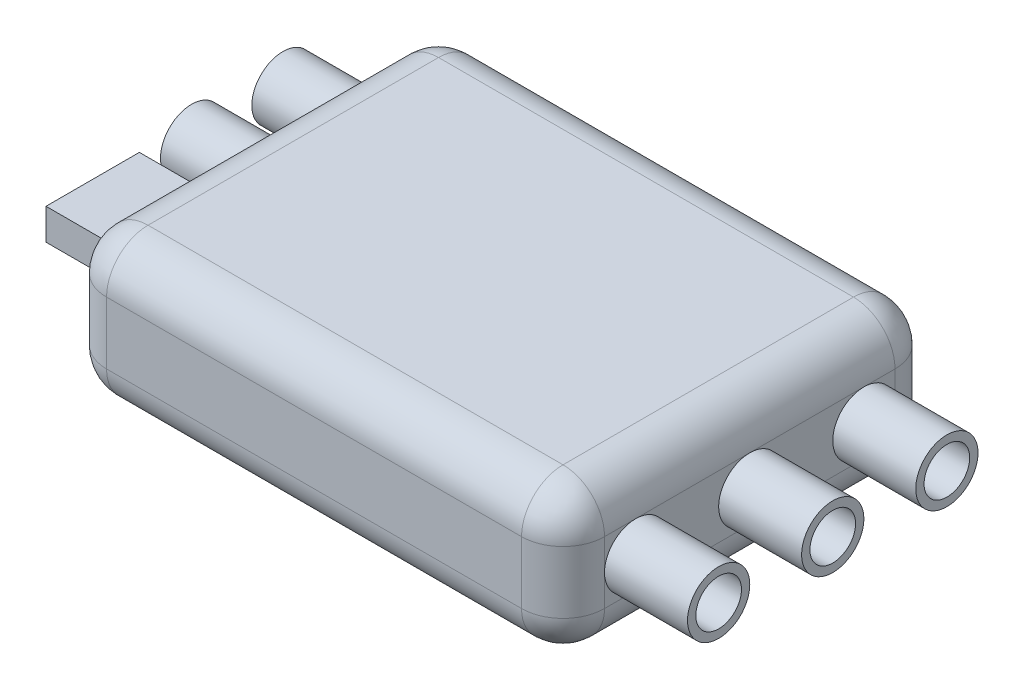
SolidWorks part; units mm, degrees
ref_plane "Front Plane" through (0, 0, 0) normal (0, 0, 1) x (1, 0, 0)
ref_plane "Top Plane" through (0, 0, 0) normal (0, 1, 0) x (1, 0, 0)
ref_plane "Right Plane" through (0, 0, 0) normal (1, 0, 0) x (0, 0, -1)
sketch "Sketch1" plane through (0, 0, 0) normal (0, 1, 0) x (1, 0, 0)
  line L1 (-10, -9) -> (10, -9)
  line L2 (-12, -7) -> (-12, 7)
  line L3 (-10, 9) -> (10, 9)
  line L4 (12, -7) -> (12, 7)
  line L5 (-12, -9) -> (12, 9) construction
  line L6 (-12, 9) -> (12, -9) construction
  arc A0 (-10, -9) -> (-12, -7) centre (-10, -7) cw
  arc A1 (10, 9) -> (12, 7) centre (10, 7) cw
  arc A2 (-12, 7) -> (-10, 9) centre (-10, 7) cw
  arc A3 (10, -9) -> (12, -7) centre (10, -7) ccw
  point P0 (0, 0)
  dimension "D3" = 2
  dimension "D4" = 2
  dimension "D1" = 24
  dimension "D2" = 18
extrude "Boss-Extrude1" add sketch "Sketch1" along normal blind 7
fillet "Fillet1" radius 2 16 edges at (0, 0, 9) (11.4142, 0, 8.4142) (12, 0, 0) (11.4142, 0, -8.4142) (0, 0, -9) (-11.4142, 0, -8.4142) (-12, 0, 0) (-11.4142, 0, 8.4142) (-12, 7, 0) (-11.4142, 7, -8.4142) (0, 7, -9) (11.4142, 7, -8.4142) (12, 7, 0) (11.4142, 7, 8.4142) (0, 7, 9) (-11.4142, 7, 8.4142)
sketch "Sketch2" plane through (12, 0, 0) normal (1, 0, 0) x (0, 0, -1)
  line L0 (7, 3.5) -> (-7, 3.5) construction
  line L1 (7, 5) -> (7, 2) construction
  line L2 (-7, 5) -> (-7, 2) construction
  circle A0 centre (5.5, 3.5) radius 1.1
  circle A1 centre (0, 3.5) radius 1.1
  circle A2 centre (-5.5, 3.5) radius 1.1
  circle A3 centre (5.5, 3.5) radius 1.5
  circle A4 centre (0, 3.5) radius 1.5
  circle A5 centre (-5.5, 3.5) radius 1.5
  dimension "D1" = 0.4
  dimension "D2" = 3
extrude "Boss-Extrude2" add sketch "Sketch2" along normal blind 4
sketch "Sketch3" plane through (-12, 0, 0) normal (-1, 0, 0) x (0, 0, 1)
  line L0 (7, 3.5) -> (-7, 3.5) construction
  line L1 (7, 5) -> (7, 2) construction
  line L2 (-7, 5) -> (-7, 2) construction
  line L4 (5.9187, 4.25) -> (1.4187, 4.25)
  line L5 (5.9187, 4.25) -> (5.9187, 2.75)
  line L6 (5.9187, 2.75) -> (1.4187, 2.75)
  line L7 (1.4187, 4.25) -> (1.4187, 2.75)
  circle A0 centre (-5.5, 3.5) radius 1.5
  circle A1 centre (-1.1, 3.5) radius 1.5
  circle A2 centre (-5.5, 3.5) radius 1.1
  circle A3 centre (-1.1, 3.5) radius 1.1
  dimension "D3" = 3
  dimension "D4" = 0.4
  dimension "D1" = 4.5
  dimension "D2" = 1.5
  dimension "D5" = 4.4
extrude "Boss-Extrude3" add sketch "Sketch3" along normal blind 4
